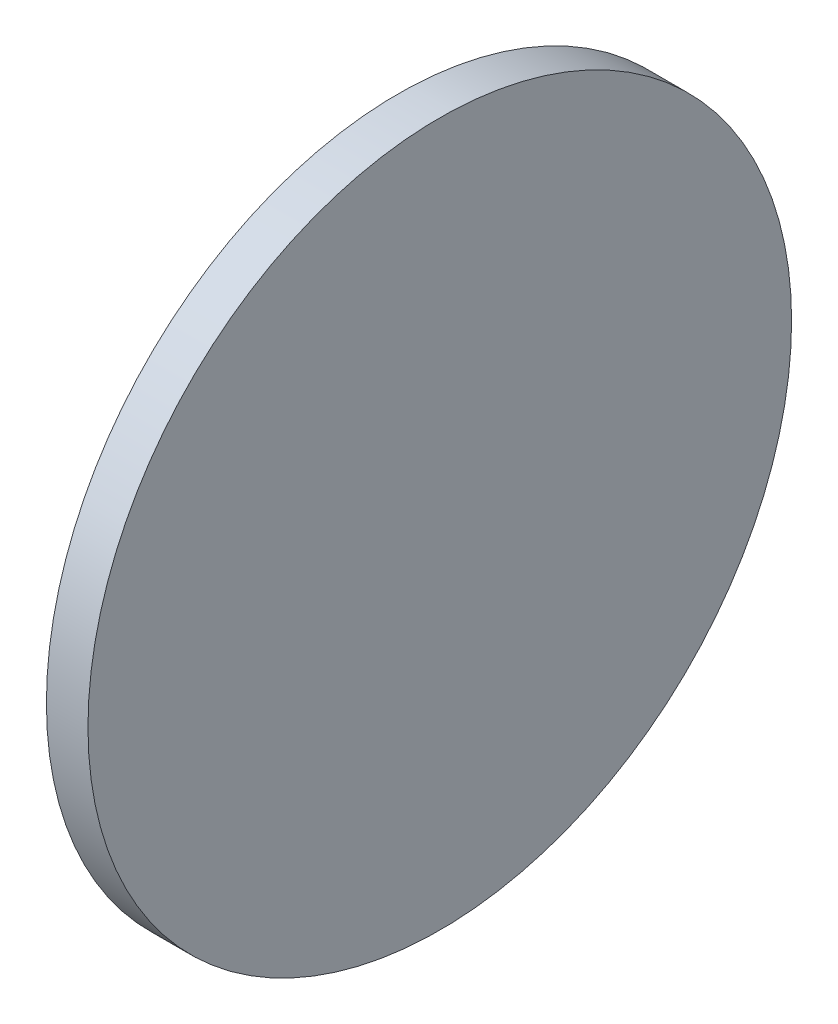
SolidWorks part; units mm, degrees
ref_plane "前视基准面" through (0, 0, 0) normal (0, 0, 1) x (1, 0, 0)
ref_plane "上视基准面" through (0, 0, 0) normal (0, 1, 0) x (1, 0, 0)
ref_plane "右视基准面" through (0, 0, 0) normal (1, 0, 0) x (0, 0, -1)
sketch "草图1" plane through (0, 0, 0) normal (0, 0, 1) x (1, 0, 0)
  line L0 (0, 25.4) -> (0, 0)
  line L2 (0, 25.4) -> (3, 25.4)
  line L3 (0, 0) -> (3, 0)
  line L4 (3, 25.4) -> (3, 0)
  dimension "D1" = 25.4
  dimension "D2" = 3
revolve "旋转2" add sketch "草图1" angle 360 about L3
